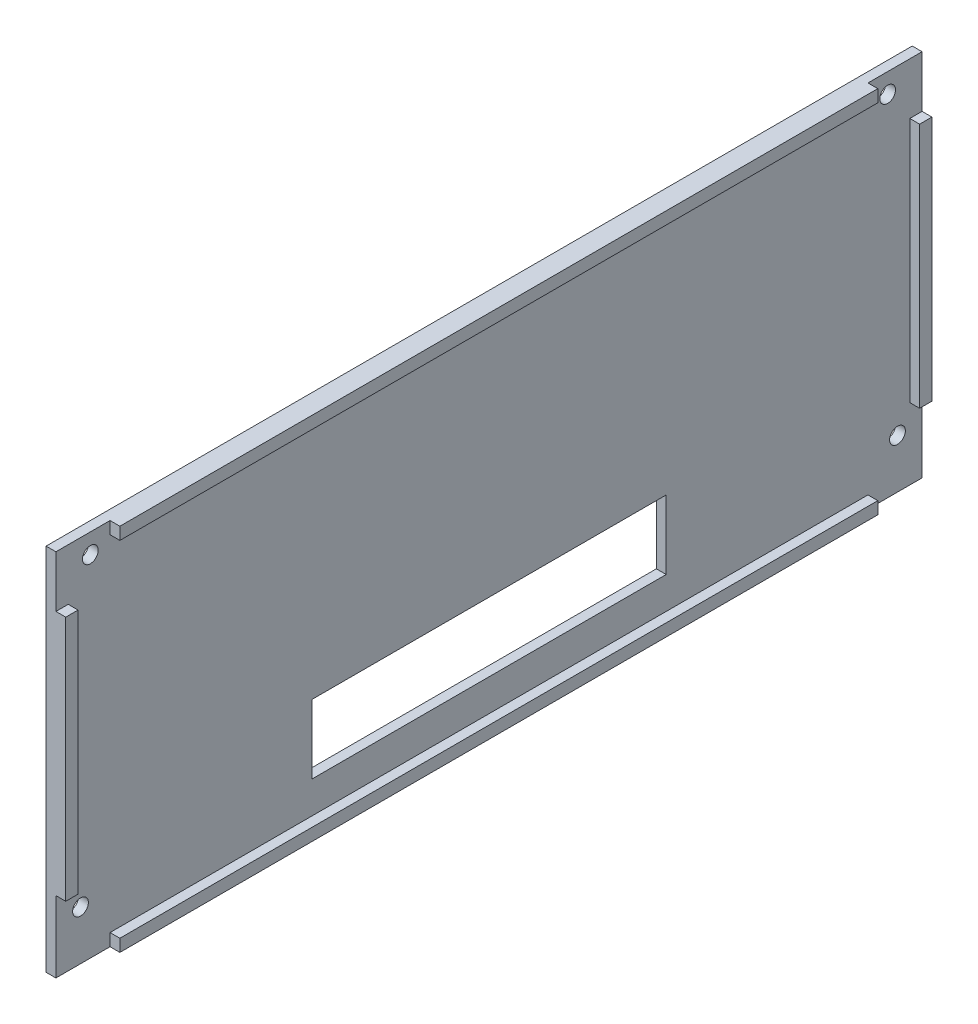
SolidWorks part; units mm, degrees
ref_plane "Front Plane" through (0, 0, 0) normal (0, 0, 1) x (1, 0, 0)
ref_plane "Top Plane" through (0, 0, 0) normal (0, 1, 0) x (1, 0, 0)
ref_plane "Right Plane" through (0, 0, 0) normal (1, 0, 0) x (0, 0, -1)
sketch "Sketch1" plane through (0, 0, 0) normal (1, 0, 0) x (0, 0, -1)
  line L0 (0, 0) -> (0, 64.2564) construction
  line L1 (-88, 37.5) -> (88, 37.5)
  line L2 (-88, 37.5) -> (-88, -37.5)
  line L3 (-88, -37.5) -> (88, -37.5)
  line L4 (88, 37.5) -> (88, -37.5)
  line L5 (-88, 37.5) -> (88, -37.5) construction
  line L6 (-88, -37.5) -> (88, 37.5) construction
  circle A0 centre (-81, 33.5) radius 1.6
  circle A1 centre (81, 33.5) radius 1.6
  circle A2 centre (-83, -27.5) radius 1.6
  circle A3 centre (83, -27.5) radius 1.6
  point P0 (0, 0)
  dimension "D3" = 7
  dimension "D5" = 5
  dimension "D1" = 176
  dimension "D2" = 75
  dimension "D4" = 4
  dimension "D6" = 10
extrude "Boss-Extrude1" add sketch "Sketch1" along normal blind 2
sketch "Sketch2" plane through (2, 0, 0) normal (1, 0, 0) x (0, 0, -1)
  line L0 (0, 0) -> (0, -60.982) construction
  line L1 (-58.6346, -28.5) -> (63.3208, -28.5) construction
  line L3 (-36, -28.5) -> (36, -28.5)
  line L4 (-36, -28.5) -> (-36, -14.5)
  line L5 (-36, -14.5) -> (36, -14.5)
  line L6 (36, -28.5) -> (36, -14.5)
  line L7 (-88, -37.5) -> (88, -37.5) construction
  dimension "D1" = 36
  dimension "D2" = 36
  dimension "D3" = 9
  dimension "D4" = 14
extrude "Cut-Extrude1" cut sketch "Sketch2" against normal blind 2
sketch "Sketch3" plane through (2, 0, 0) normal (1, 0, 0) x (0, 0, -1)
  line L0 (0, 0) -> (0, -67.6738) construction
  line L1 (-88, -37.5) -> (88, -37.5) construction
  line L2 (0, 0) -> (95.959, 0) construction
  line L3 (-77, -37.5) -> (77, -37.5)
  line L4 (-77, -37.5) -> (-77, -35)
  line L5 (-77, -35) -> (77, -35)
  line L6 (77, -37.5) -> (77, -35)
  line L7 (-77, 35) -> (77, 35)
  line L8 (77, 37.5) -> (77, 35)
  line L9 (-77, 37.5) -> (77, 37.5)
  line L10 (-77, 37.5) -> (-77, 35)
  point P9 (-77, -36.25)
  dimension "D1" = 2.5
  dimension "D2" = 77
  dimension "D3" = 77
extrude "Boss-Extrude2" add sketch "Sketch3" along normal blind 2
sketch "Sketch4" plane through (2, 0, 0) normal (1, 0, 0) x (0, 0, -1)
  line L0 (-88, 37.5) -> (-88, -37.5) construction
  line L1 (-88, 27) -> (-85.5, 27)
  line L2 (-88, 27) -> (-88, -23)
  line L3 (-88, -23) -> (-85.5, -23)
  line L4 (-85.5, 27) -> (-85.5, -23)
  line L5 (0, 0) -> (-103.8414, 0) construction
  line L6 (0, 0) -> (0, 44.2972) construction
  line L9 (88, -23) -> (85.5, -23)
  line L10 (85.5, 27) -> (85.5, -23)
  line L11 (88, 27) -> (85.5, 27)
  line L12 (88, 27) -> (88, -23)
  dimension "D1" = 2.5
  dimension "D2" = 27
  dimension "D3" = 23
extrude "Boss-Extrude3" add sketch "Sketch4" along normal blind 2
